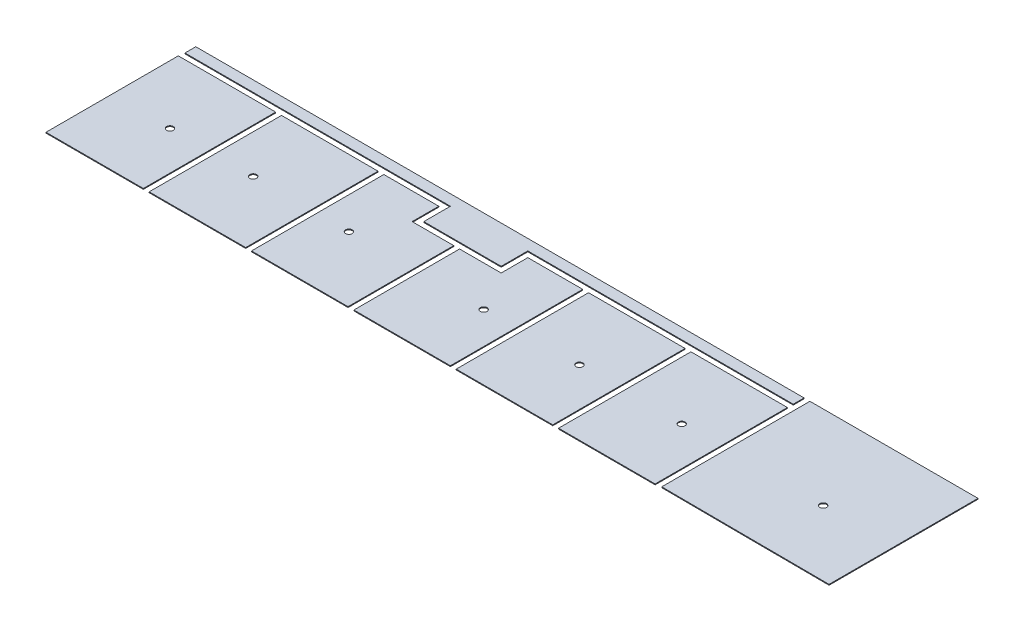
SolidWorks part; units mm, degrees
ref_plane "Front Plane" through (0, 0, 0) normal (0, 0, 1) x (1, 0, 0)
ref_plane "Top Plane" through (0, 0, 0) normal (0, 1, 0) x (1, 0, 0)
ref_plane "Right Plane" through (0, 0, 0) normal (1, 0, 0) x (0, 0, -1)
ref_plane "Plane1" through (0, 2266.95, 0) normal (0, 1, 0) x (1, 0, 0)
sketch "Sketch1" plane through (0, 2266.95, 0) normal (0, 1, 0) x (1, 0, 0)
  line L80 (50.8, 2146.3) -> (50.8, 2311.4)
  line L81 (11988.8, 2311.4) -> (38.1, 2311.4) construction
  line L82 (50.8, 2311.4) -> (9334.5, 2311.4)
  line L83 (9334.5, 2311.4) -> (9334.5, 2146.3)
  line L90 (9334.5, 2146.3) -> (5283.2, 2146.3)
  line L91 (5283.2, 2146.3) -> (5283.2, 1739.9)
  line L92 (5283.2, 1739.9) -> (4102.1, 1739.9)
  line L93 (4102.1, 1739.9) -> (4102.1, 2146.3)
  line L94 (4102.1, 2146.3) -> (50.8, 2146.3)
  line L95 (9423.4, 2146.3) -> (9423.4, 2311.4)
  line L96 (9423.4, 2311.4) -> (11988.8, 2311.4)
  line L97 (11988.8, 2311.4) -> (11988.8, 38.1)
  line L98 (11988.8, 38.1) -> (9423.4, 50.8)
  line L103 (9423.4, 50.8) -> (9423.4, 2146.3)
  line L108 (38.1, 38.1) -> (11988.8, 38.1) construction
  line L109 (9334.5, 2057.4) -> (7861.3, 2057.4)
  line L110 (9334.5, 2057.4) -> (9334.5, 38.1)
  line L115 (9334.5, 38.1) -> (7861.3, 38.1)
  line L116 (7861.3, 2057.4) -> (7861.3, 38.1)
  line L117 (7772.4, 2057.4) -> (6299.2, 2057.4)
  line L118 (7772.4, 2057.4) -> (7772.4, 38.1)
  line L119 (7772.4, 38.1) -> (6299.2, 38.1)
  line L120 (6299.2, 2057.4) -> (6299.2, 38.1)
  line L121 (3086.1, 2057.4) -> (1612.9, 2057.4)
  line L122 (3086.1, 2057.4) -> (3086.1, 38.1)
  line L127 (3086.1, 38.1) -> (1612.9, 38.1)
  line L128 (1612.9, 2057.4) -> (1612.9, 38.1)
  line L129 (3175, 2057.4) -> (4013.2, 2057.4)
  line L130 (1524, 2057.4) -> (38.1, 2057.4)
  line L131 (1524, 2057.4) -> (1524, 38.1)
  line L132 (1524, 38.1) -> (38.1, 38.1)
  line L133 (38.1, 2057.4) -> (38.1, 38.1)
  line L134 (4013.2, 2057.4) -> (4013.2, 1651)
  line L135 (4013.2, 1651) -> (4648.2, 1651)
  line L136 (4648.2, 1651) -> (4648.2, 38.1)
  line L137 (4648.2, 38.1) -> (3175, 38.1)
  line L138 (3175, 38.1) -> (3175, 2057.4)
  line L139 (4737.1, 1651) -> (4737.1, 38.1)
  line L140 (4737.1, 38.1) -> (6210.3, 38.1)
  line L141 (6210.3, 38.1) -> (6210.3, 2057.4)
  line L142 (6210.3, 2057.4) -> (5372.1, 2057.4)
  line L143 (5372.1, 2057.4) -> (5372.1, 1651)
  line L144 (5372.1, 1651) -> (4737.1, 1651)
extrude "Boss-Extrude1" add sketch "Sketch1" along normal up to vertex (12.7 mm away) contours L130 L133 L132 L131 | L121 L128 L127 L122 | L94 L93 L92 L91 L90 L83 L82 L80 | L138 L137 L136 L135 L134 L129 | L143 L144 L139 L140 L141 L142 | L117 L120 L119 L118 | L109 L116 L115 L110 | L103 L98 L97 L96 L95
sketch "Sketch3" plane through (0, 2266.95, 0) normal (0, 1, 0) x (1, 0, 0)
  line L0 (1568.45, 2330.45) -> (1568.45, 19.05) construction
  line L1 (3130.55, 2330.45) -> (3130.55, 19.05) construction
  line L2 (4692.65, 1695.45) -> (4692.65, 19.05) construction
  line L3 (4057.65, 1695.45) -> (5327.65, 1695.45) construction
  line L4 (6254.75, 2330.45) -> (6254.75, 19.05) construction
  line L5 (7816.85, 2330.45) -> (7816.85, 19.05) construction
  line L6 (9378.95, 2330.45) -> (9378.95, 19.05) construction
  line L7 (933.45, 1035.05) -> (11988.8, 1035.05) construction
  line L8 (11988.8, 2311.4) -> (11988.8, 38.1) construction
  circle A0 centre (933.45, 1035.05) radius 50.8
  circle A1 centre (2203.45, 1035.05) radius 50.8
  circle A2 centre (3663.95, 1035.05) radius 50.8
  circle A3 centre (5721.35, 1035.05) radius 50.8
  circle A4 centre (7181.85, 1035.05) radius 50.8
  circle A5 centre (8743.95, 1035.05) radius 50.8
  circle A6 centre (10902.95, 1035.05) radius 50.8
  dimension "D1" = 101.6
  dimension "D2" = 635
  dimension "D3" = 635
  dimension "D4" = 1016
  dimension "D5" = 533.4
  dimension "D6" = 533.4
  dimension "D7" = 635
  dimension "D8" = 635
  dimension "D9" = 1524
extrude "Cut-Extrude1" cut sketch "Sketch3" along normal up to next (12.7 mm away) contours A0 | A1 | A3 | A2 | A4 | A5 | A6
